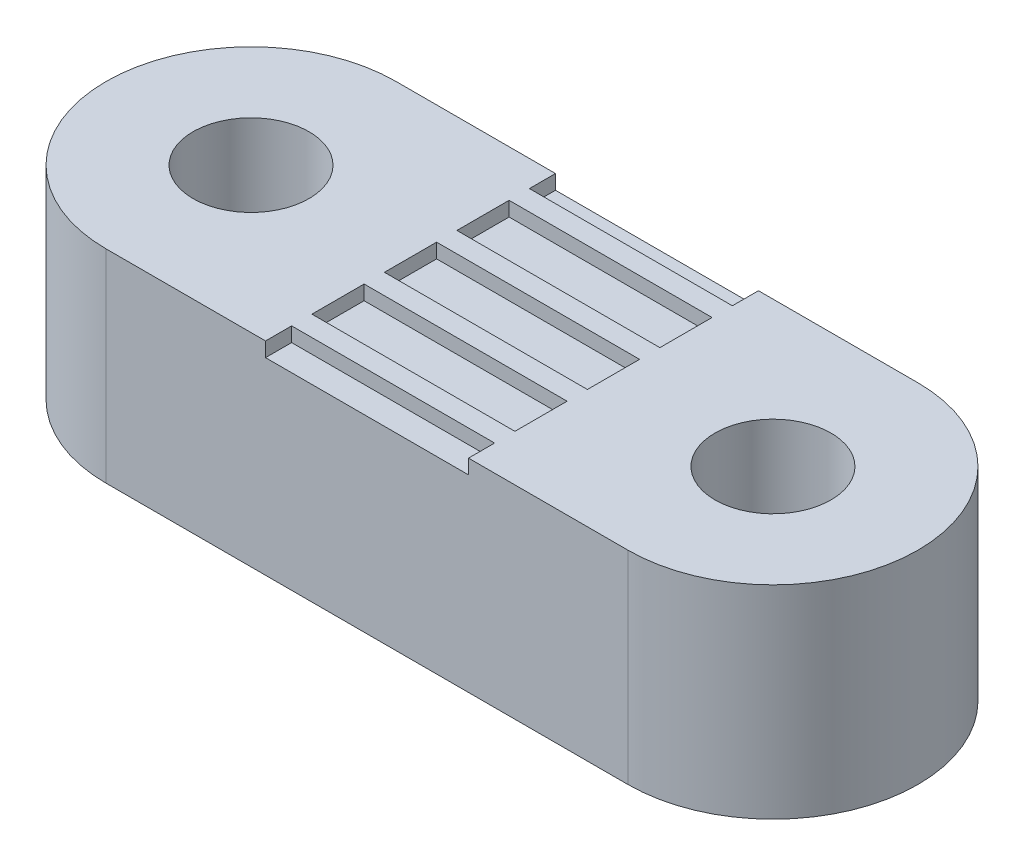
SolidWorks part; units mm, degrees
ref_plane "Front Plane" through (0, 0, 0) normal (0, 0, 1) x (1, 0, 0)
ref_plane "Top Plane" through (0, 0, 0) normal (0, 1, 0) x (1, 0, 0)
ref_plane "Right Plane" through (0, 0, 0) normal (1, 0, 0) x (0, 0, -1)
sketch "Sketch1" plane through (0, 0, 0) normal (0, 1, 0) x (1, 0, 0)
  line L0 (-9, 0) -> (9, 0) construction
  line L1 (-9, 5) -> (9, 5)
  line L2 (-9, -5) -> (9, -5)
  arc A0 (-9, 5) -> (-9, -5) centre (-9, 0) ccw
  arc A1 (9, -5) -> (9, 5) centre (9, 0) ccw
  circle A2 centre (-9, 0) radius 2
  circle A3 centre (9, 0) radius 2
  point P2 (0, 0)
  dimension "D1" = 4
  dimension "D2" = 10
  dimension "D3" = 9
extrude "Boss-Extrude1" add sketch "Sketch1" along normal blind 7
sketch "Sketch2" plane through (0, 7, 0) normal (0, 1, 0) x (1, 0, 0)
  line L4 (-3.5, 0.9) -> (3.5, 0.9)
  line L5 (-3.5, 0.9) -> (-3.5, -0.9)
  line L6 (-3.5, -0.9) -> (3.5, -0.9)
  line L7 (3.5, 0.9) -> (3.5, -0.9)
  line L8 (-3.5, 0.9) -> (3.5, -0.9) construction
  line L9 (-3.5, -0.9) -> (3.5, 0.9) construction
  point P0 (0, 0)
  dimension "D1" = 1.8
  dimension "D2" = 7
extrude "Cut-Extrude1" cut sketch "Sketch2" against normal blind 0.5
pattern_linear "LPattern1" count 3 spacing 2.5 along (0, 0, 1) count 3 spacing 2.5 along (0, 0, -1) of "Cut-Extrude1"
